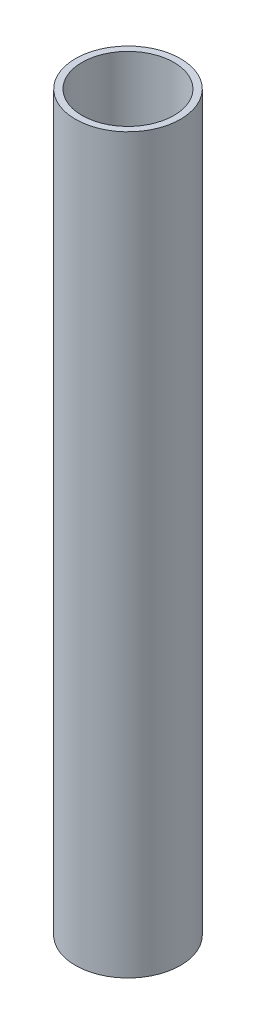
SolidWorks part; units mm, degrees
material "Acrylic (Medium-high impact)"
ref_plane "Front Plane" through (0, 0, 0) normal (0, 0, 1) x (1, 0, 0)
ref_plane "Top Plane" through (0, 0, 0) normal (0, 1, 0) x (1, 0, 0)
ref_plane "Right Plane" through (0, 0, 0) normal (1, 0, 0) x (0, 0, -1)
sketch "Sketch1" plane through (0, 0, 0) normal (0, 1, 0) x (1, 0, 0)
  circle A0 centre (0, 0) radius 10.668
  circle A1 centre (0, 0) radius 12.192
  dimension "D1" = 1.524
extrude "Boss-Extrude1" add sketch "Sketch1" along normal blind 170
